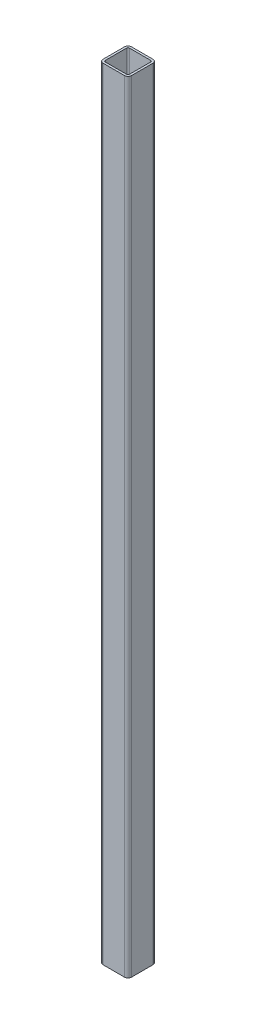
SolidWorks part; units mm, degrees
ref_plane "Спереди" through (0, 0, 0) normal (0, 0, 1) x (1, 0, 0)
ref_plane "Сверху" through (0, 0, 0) normal (0, 1, 0) x (1, 0, 0)
ref_plane "Справа" through (0, 0, 0) normal (1, 0, 0) x (0, 0, -1)
sketch "Эскиз1" plane through (0, 0, 0) normal (0, 1, 0) x (1, 0, 0)
  line L1 (-15, 20) -> (15, 20)
  line L2 (-20, 15) -> (-20, -15)
  line L3 (-15, -20) -> (15, -20)
  line L4 (20, 15) -> (20, -15)
  line L5 (-20, 20) -> (20, -20) construction
  line L6 (-20, -20) -> (20, 20) construction
  arc A0 (-20, -15) -> (-15, -20) centre (-15, -15) ccw
  arc A1 (15, -20) -> (20, -15) centre (15, -15) ccw
  arc A2 (15, 20) -> (20, 15) centre (15, 15) cw
  arc A3 (-15, 20) -> (-20, 15) centre (-15, 15) ccw
  point P0 (0, 0)
  dimension "D1" = 5
  dimension "D2" = 40
  dimension "D3" = 40
extrude "Вытянуть-Тонкостенный1" add sketch "Эскиз1" along normal blind 1100 thin
